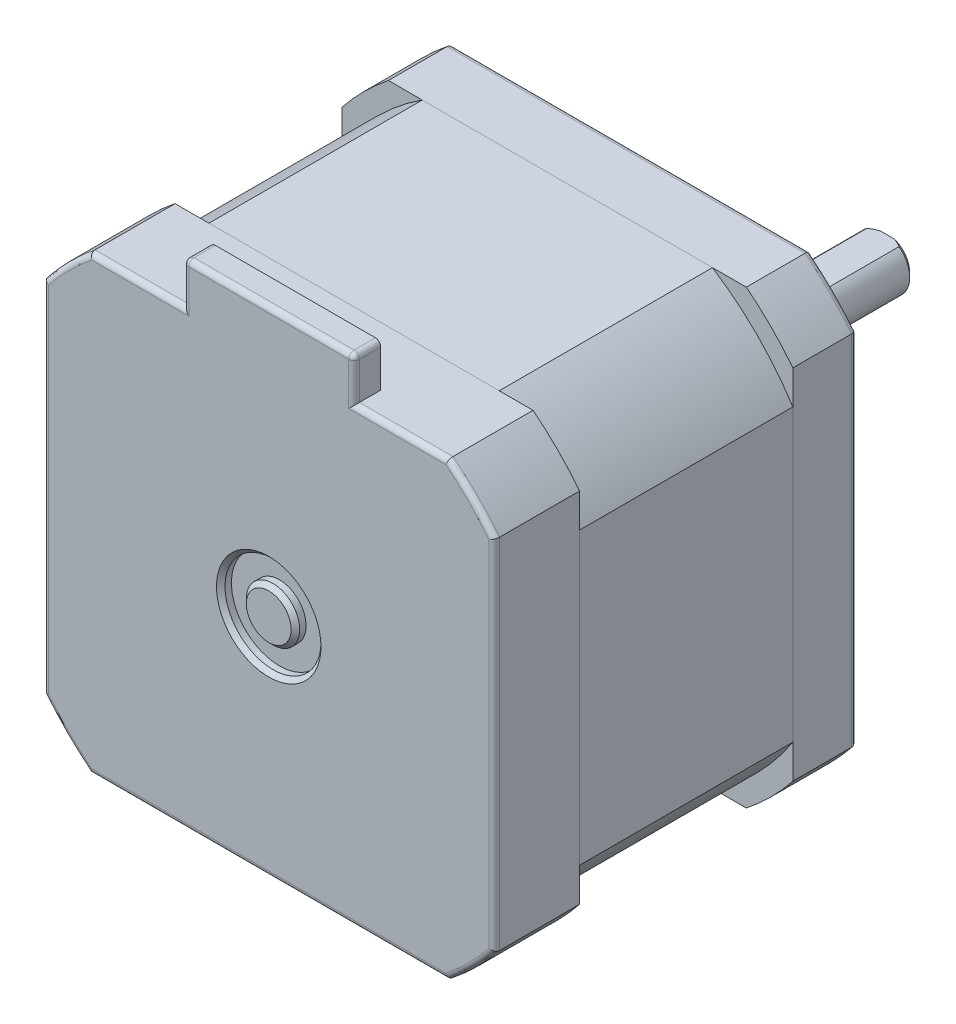
SolidWorks part; units mm, degrees
ref_plane "Plan de face" through (0, 0, 0) normal (0, 0, 1) x (1, 0, 0)
ref_plane "Plan de dessus" through (0, 0, 0) normal (0, 1, 0) x (1, 0, 0)
ref_plane "Plan de droite" through (0, 0, 0) normal (1, 0, 0) x (0, 0, -1)
sketch "Esquisse1" plane through (0, 0, 0) normal (0, 0, 1) x (1, 0, 0)
  line L0 (21.15, 16.7833) -> (21.15, -16.7833)
  line L1 (-21.15, 21.15) -> (21.15, 21.15) construction
  line L2 (-21.15, 21.15) -> (-21.15, -21.15) construction
  line L3 (-21.15, -21.15) -> (21.15, -21.15) construction
  line L4 (21.15, 21.15) -> (21.15, -21.15) construction
  line L5 (-21.15, 21.15) -> (21.15, -21.15) construction
  line L6 (-21.15, -21.15) -> (21.15, 21.15) construction
  line L7 (16.7833, -21.15) -> (-16.7833, -21.15)
  line L8 (-21.15, -16.7833) -> (-21.15, 16.7833)
  line L9 (-16.7833, 21.15) -> (16.7833, 21.15)
  arc A0 (-16.7833, 21.15) -> (-21.15, 16.7833) centre (0, 0) ccw
  arc A1 (21.15, 16.7833) -> (16.7833, 21.15) centre (0, 0) ccw
  arc A2 (-21.15, -16.7833) -> (-16.7833, -21.15) centre (0, 0) ccw
  arc A3 (16.7833, -21.15) -> (21.15, -16.7833) centre (0, 0) ccw
  point P0 (0, 0)
  dimension "D2" = 54
  dimension "D1" = 42.3
extrude "Boss.-Extru.1" add sketch "Esquisse1" along normal blind 6
sketch "Esquisse2" plane through (0, 0, 6) normal (0, 0, 1) x (1, 0, 0)
  line L23 (-13.6088, 21.15) -> (13.6088, 21.15)
  line L24 (16.7833, 21.15) -> (-16.7833, 21.15) construction
  line L25 (21.15, 13.6088) -> (21.15, -13.6088)
  line L26 (21.15, -16.7833) -> (21.15, 16.7833) construction
  line L27 (13.6088, -21.15) -> (-13.6088, -21.15)
  line L28 (-16.7833, -21.15) -> (16.7833, -21.15) construction
  line L29 (-21.15, -13.6088) -> (-21.15, 13.6088)
  line L30 (-21.15, 16.7833) -> (-21.15, -16.7833) construction
  arc A60 (-13.6088, 21.15) -> (-21.15, 13.6088) centre (0, 0) ccw
  arc A61 (21.15, 16.7833) -> (16.7833, 21.15) centre (0, 0) ccw construction
  arc A62 (21.15, 13.6088) -> (13.6088, 21.15) centre (0, 0) ccw
  arc A63 (13.6088, -21.15) -> (21.15, -13.6088) centre (0, 0) ccw
  arc A64 (-21.15, -13.6088) -> (-13.6088, -21.15) centre (0, 0) ccw
  dimension "D1" = 1.85
extrude "Boss.-Extru.2" add sketch "Esquisse2" along normal blind 20 separate body
sketch "Esquisse3" plane through (0, 0, 26) normal (0, 0, 1) x (1, 0, 0)
  line L0 (-16.7833, -21.15) -> (16.7833, -21.15) construction
  line L1 (21.15, -16.7833) -> (21.15, 16.7833) construction
  line L2 (16.7833, 21.15) -> (-16.7833, 21.15) construction
  line L3 (-21.15, 16.7833) -> (-21.15, -16.7833) construction
  line L4 (-16.7833, -21.15) -> (16.7833, -21.15)
  line L5 (21.15, -16.7833) -> (21.15, 16.7833)
  line L6 (16.7833, 21.15) -> (-16.7833, 21.15)
  line L7 (-21.15, 16.7833) -> (-21.15, -16.7833)
  arc A0 (-21.15, -16.7833) -> (-16.7833, -21.15) centre (0, 0) ccw construction
  arc A1 (16.7833, -21.15) -> (21.15, -16.7833) centre (0, 0) ccw construction
  arc A2 (21.15, 16.7833) -> (16.7833, 21.15) centre (0, 0) ccw construction
  arc A3 (-16.7833, 21.15) -> (-21.15, 16.7833) centre (0, 0) ccw construction
  arc A4 (-21.15, -16.7833) -> (-16.7833, -21.15) centre (0, 0) ccw
  arc A5 (16.7833, -21.15) -> (21.15, -16.7833) centre (0, 0) ccw
  arc A6 (21.15, 16.7833) -> (16.7833, 21.15) centre (0, 0) ccw
  arc A7 (-16.7833, 21.15) -> (-21.15, 16.7833) centre (0, 0) ccw
extrude "Boss.-Extru.3" add sketch "Esquisse3" along normal blind 8 separate body
sketch "Esquisse4" plane through (0, 21.15, 0) normal (0, 1, 0) x (1, 0, 0)
  line L0 (16.7833, -34) -> (-16.7833, -34) construction
  line L1 (8, -34) -> (-8, -34)
  line L2 (8, -34) -> (8, -31.5)
  line L3 (8, -31.5) -> (-8, -31.5)
  line L4 (-8, -34) -> (-8, -31.5)
  line L5 (0, 0) -> (0, -31.5) construction
  dimension "D1" = 2.5
  dimension "D2" = 16
extrude "Boss.-Extru.4" add sketch "Esquisse4" along normal blind 4
sketch "Esquisse5" plane through (0, 0, 0) normal (1, 0, 0) x (0, 0, -1)
  line L0 (0, 0) -> (-78.698, 0) construction
  line L2 (2, 11) -> (0, 11)
  line L3 (2, 11) -> (2, 4.5)
  line L4 (2, 4.5) -> (0, 4.5)
  line L5 (0, 11) -> (0, 4.5)
  line L6 (0, -16.7833) -> (0, 16.7833) construction
  line L7 (24, 0) -> (0, 0)
  line L8 (24, 0) -> (24, 2.5)
  line L9 (24, 2.5) -> (0, 2.5)
  line L10 (0, 0) -> (0, 2.5)
  dimension "D1" = 2
  dimension "D2" = 22
  dimension "D3" = 9
  dimension "D4" = 5
  dimension "D5" = 24
revolve "Révolution1" add sketch "Esquisse5" angle 360 about L0
fillet "Congé1" radius 0.5 14 edges at (-21.15, 0, 34) (-19.0919, 19.0919, 34) (-12.3916, 21.15, 34) (-8, 23.15, 34) (0, 25.15, 34) (8, 23.15, 34) (12.3916, 21.15, 34) (19.0919, 19.0919, 34) (21.15, 0, 34) (19.0919, -19.0919, 34) (0, -21.15, 34) (-19.0919, -19.0919, 34) (-8, 25.15, 32.75) (8, 25.15, 32.75)
fillet "Congé2" radius 0.5 8 edges at (-19.0919, 19.0919, 0) (-21.15, 0, 0) (-19.0919, -19.0919, 0) (0, -21.15, 0) (19.0919, -19.0919, 0) (21.15, 0, 0) (0, 21.15, 0) (19.0919, 19.0919, 0)
chamfer "Chanfrein1" distance 0.4 angle 45 1 edges at (-2.5, 0, -24)
chamfer "Chanfrein2" distance 0.4 angle 45 1 edges at (-4.5, 0, -2)
sketch "Esquisse6" plane through (0, 0, 0) normal (1, 0, 0) x (0, 0, -1)
  line L0 (0, -2.5) -> (23.6, -2.5) construction
  line L1 (24, 2.5) -> (9, 2.5)
  line L2 (24, 2.5) -> (24, 2)
  line L3 (24, 2) -> (9, 2)
  line L4 (9, 2.5) -> (9, 2)
  line L5 (24, -2.1) -> (24, 2.1) construction
  line L6 (23.6, 2.5) -> (0, 2.5) construction
  dimension "D1" = 4.5
  dimension "D2" = 15
extrude "Enlèv. mat.-Extru.1" cut sketch "Esquisse6" against normal through all both and the other way through all
sketch "Esquisse7" plane through (0, 0, 34) normal (0, 0, 1) x (1, 0, 0)
  circle A0 centre (0, 0) radius 2.5
  circle A1 centre (0, 0) radius 4.5
  dimension "D1" = 5
  dimension "D2" = 9
extrude "Enlèv. mat.-Extru.2" cut sketch "Esquisse7" against normal blind 1
chamfer "Chanfrein3" distance 0.4 angle 45 2 edges at (4.5, 0, 34) (2.5, 0, 34)
hole_wizard "Trou taraudé M31" positions "Esquisse8" profile "Esquisse9" tap size "M3" standard "ISO"
sketch "Esquisse8" plane through (0, 0, 0) normal (0, 0, -1) x (-1, 0, 0)
  line L0 (-15.5, 15.5) -> (15.5, 15.5) construction
  line L1 (15.5, 15.5) -> (15.5, -15.5) construction
  line L2 (15.5, -15.5) -> (-15.5, -15.5) construction
  line L3 (-15.5, -15.5) -> (-15.5, 15.5) construction
  circle A0 centre (0, 0) radius 21.9203 construction
  point P5 (-15.5, 15.5)
  point P6 (15.5, 15.5)
  point P7 (15.5, -15.5)
  point P8 (-15.5, -15.5)
  dimension "D1" = 31
sketch "Esquisse9" plane through (15.5, -15.5, 0) normal (1, 0, 0) x (0, 1, 0)
  line L0 (0, 0) -> (0, 5.7511)
  line L1 (0, 5.7511) -> (1.25, 5)
  line L2 (1.25, 5) -> (1.25, 0)
  line L5 (1.25, 0) -> (0, 0)
  line L10 (0, 5.7511) -> (-1.25, 5) construction
  line L11 (0, -6.35) -> (0, 107.95) construction
  dimension "Diamètre du trou pour taraudage" = 2.5
  dimension "Profondeur du trou pour taraudage" = 5
  dimension "Angle de pointe" = 118
cosmetic thread "Filetage de perçage1" parameters "D1"=5, "D2"=3
cosmetic thread "Filetage de perçage2" parameters "D1"=5, "D2"=3
cosmetic thread "Filetage de perçage3" parameters "D1"=5, "D2"=3
cosmetic thread "Filetage de perçage4" parameters "D1"=5, "D2"=3
